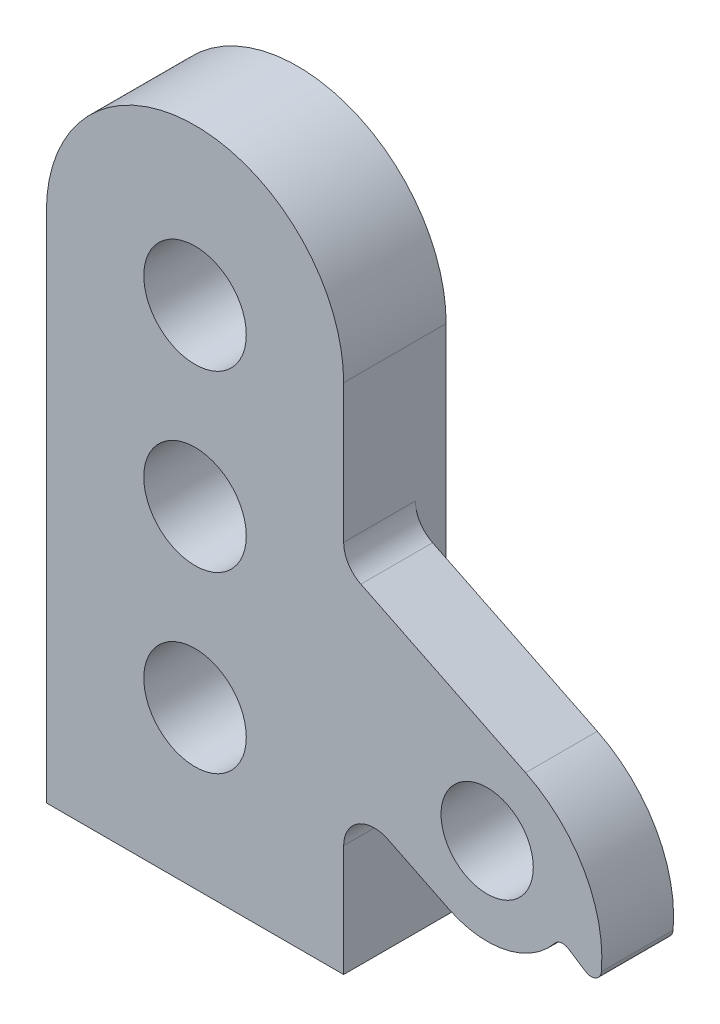
SolidWorks part; units mm, degrees
ref_plane "Plan de face" through (0, 0, 0) normal (0, 0, 1) x (1, 0, 0)
ref_plane "Plan de dessus" through (0, 0, 0) normal (0, 1, 0) x (1, 0, 0)
ref_plane "Plan de droite" through (0, 0, 0) normal (1, 0, 0) x (0, 0, -1)
sketch "Esquisse1" plane through (0, 0, 0) normal (0, 0, 1) x (1, 0, 0)
  line L0 (0, 7.3) -> (28.5, -6.7) construction
  line L1 (-14.5, -25) -> (14.5, -25)
  line L2 (-14.5, -25) -> (-14.5, 25)
  line L4 (14.5, -25) -> (14.5, 25) construction
  line L5 (-14.5, -25) -> (14.5, 25) construction
  line L6 (-14.5, 25) -> (14.5, -25) construction
  line L7 (32.2477, 0.9292) -> (16.1773, 8.8234)
  line L8 (24.7523, -14.3292) -> (18.8227, -11.4164)
  line L9 (14.5, -25) -> (14.5, -14.1091)
  line L10 (14.5, 11.5161) -> (14.5, 25)
  line L11 (36.4198, -11.8504) -> (38.0965, -12.9407)
  circle A2 centre (0, 7.3) radius 5
  arc A3 (-14.5, 25) -> (14.5, 25) centre (0, 25) cw
  circle A4 centre (28.5, -6.7) radius 4.5
  arc A5 (24.7523, -14.3292) -> (35.0984, -12.0583) centre (28.5, -6.7) ccw
  arc A6 (14.5, -14.1091) -> (18.8227, -11.4164) centre (17.5, -14.1091) cw
  arc A7 (14.5, 11.5161) -> (16.1773, 8.8234) centre (17.5, 11.5161) ccw
  arc A8 (32.2477, 0.9292) -> (39.6378, -12.1905) centre (26.379, -11.0177) cw
  arc A9 (39.6378, -12.1905) -> (38.0965, -12.9407) centre (38.6417, -12.1024) cw
  arc A10 (35.0984, -12.0583) -> (36.4198, -11.8504) centre (35.8747, -12.6887) cw
  point P0 (0, 0)
  point P17 (14.5, -9.293)
  point P20 (14.5, 9.6474)
  point P26 (39.3982, -13.7872)
  point P29 (35.6258, -11.334)
  dimension "D2" = 14.5
  dimension "D3" = 29
  dimension "D4" = 17.7
  dimension "D5" = 14.5
  dimension "D6" = 10
  dimension "D7" = 50
  dimension "D8" = 9
  dimension "D11" = 8.5
  dimension "D12" = 3
  dimension "D13" = 3
  dimension "D15" = 1
  dimension "D16" = 1
  dimension "D1" = 29
  dimension "D9" = 14
  dimension "D10" = 28.5
  dimension "D14" = 4.5
  dimension "D17" = 2
extrude "Boss.-Extru.1" add sketch "Esquisse1" along normal blind 7
sketch "Esquisse4" plane through (0, 0, 0) normal (0, 0, -1) x (-1, 0, 0)
  line L0 (14.5, 25) -> (14.5, -25)
  line L1 (14.5, -25) -> (-14.5, -25)
  line L2 (-14.5, -25) -> (-14.5, 25)
  arc A0 (-14.5, 25) -> (14.5, 25) centre (0, 25) cw
  circle A1 centre (0, 7.3) radius 5
  dimension "D1" = 10
extrude "Boss.-Extru.3" add sketch "Esquisse4" along normal blind 3
sketch "Esquisse5" plane through (0, 0, -3) normal (0, 0, -1) x (-1, 0, 0)
  line L0 (14.5, -25) -> (-14.5, -25)
  line L1 (14.5, -25) -> (14.5, -18)
  line L2 (-14.5, -25) -> (-14.5, -18)
  line L3 (14.5, -18) -> (-14.5, -18)
  dimension "D1" = 7
extrude "Boss.-Extru.4" add sketch "Esquisse5" along normal blind 8
sketch "Esquisse6" plane through (0, -25, 0) normal (0, -1, 0) x (1, 0, 0)
  line L0 (14.5, -11) -> (-14.5, -11) construction
  circle A0 centre (0, -7) radius 3
  dimension "D1" = 6
  dimension "D2" = 4
extrude "Enlèv. mat.-Extru.1" cut sketch "Esquisse6" against normal through all
sketch "Esquisse8" plane through (0, 0, 7) normal (0, 0, 1) x (1, 0, 0)
  line L0 (-14.5, -25) -> (-14.5, 25) construction
  circle A0 centre (0, -9.7) radius 5
  circle A1 centre (0, 24.3) radius 5
  circle A3 centre (0, 7.3) radius 5 construction
  point P6 (0, 0)
  point P9 (0, 0)
  point P10 (0.0034, -5.8197)
  dimension "D1" = 10
  dimension "D2" = 10
  dimension "D5" = 17
  dimension "D3" = 14.5
  dimension "D4" = 14.5
  dimension "D6" = 17
extrude "Enlèv. mat.-Extru.2" cut sketch "Esquisse8" against normal through all
